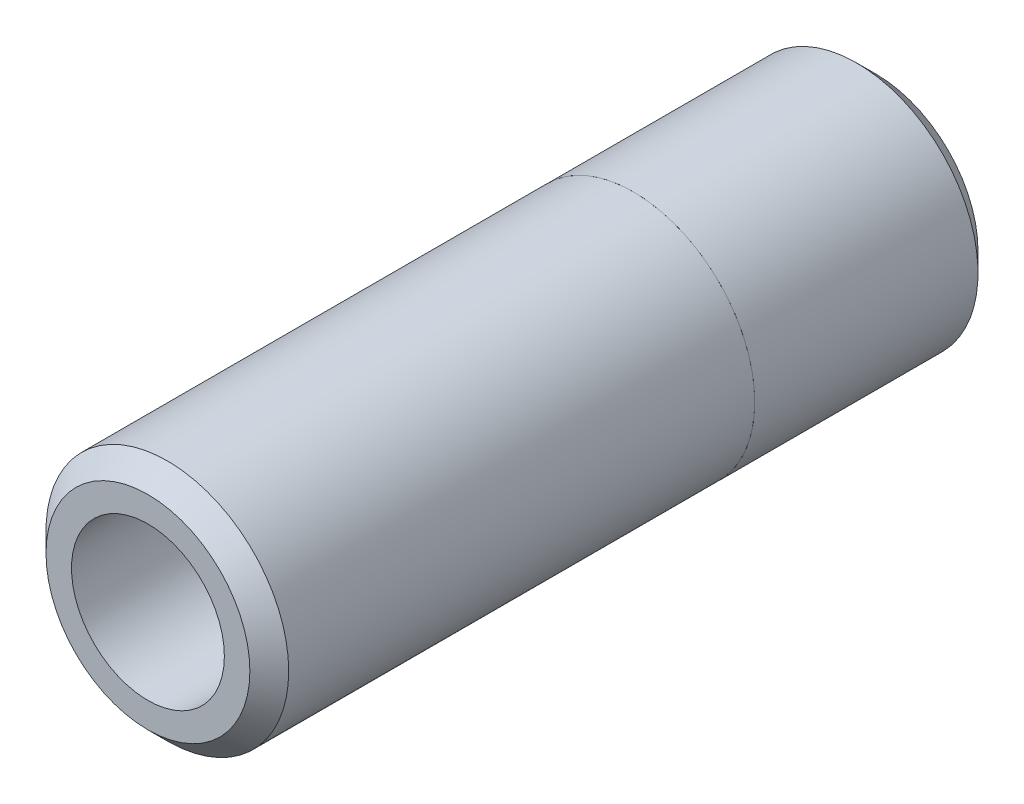
SolidWorks part; units mm, degrees
material "Delrin 2700 NC010, Low Viscosity Acetal Copolymer (SS)"
ref_plane "Front Plane" through (0, 0, 0) normal (0, 0, 1) x (1, 0, 0)
ref_plane "Top Plane" through (0, 0, 0) normal (0, 1, 0) x (1, 0, 0)
ref_plane "Right Plane" through (0, 0, 0) normal (1, 0, 0) x (0, 0, -1)
sketch "Sketch1" plane through (0, 0, 0) normal (0, 0, 1) x (1, 0, 0)
  circle A0 centre (0, 0) radius 4.7625
  dimension "D1" = 9.525
extrude "Side With Hole" add sketch "Sketch1" along normal blind 19.05
sketch "Sketch2" plane through (0, 0, 0) normal (0, 0, -1) x (-1, 0, 0)
  circle A1 centre (0, 0) radius 4.7625
  circle A2 centre (0, 0) radius 4.7625
  dimension "D1" = 0
extrude "Side Without Hole" add sketch "Sketch2" along normal blind 9.525 separate body
hole_wizard "Ø6.0 (6) Diameter Hole1" positions "Sketch3" profile "Sketch4" hole size "Ø6.0" standard "ANSI Metric"
sketch "Sketch3" plane through (0, 0, 19.05) normal (0, 0, 1) x (1, 0, 0)
  point P0 (0, 0)
sketch "Sketch4" plane through (0, 0, 19.05) normal (1, 0, 0) x (0, -1, 0)
  line L0 (0, 0) -> (0, 22.7576)
  line L1 (0, 22.7576) -> (3, 20.955)
  line L2 (3, 20.955) -> (3, 0)
  line L5 (3, 0) -> (0, 0)
  line L10 (0, 22.7576) -> (-3, 20.955) construction
  line L11 (0, -6.35) -> (0, 107.95) construction
  dimension "Hole Dia." = 6
  dimension "Hole Depth" = 20.955
  dimension "Drill Angle" = 118
chamfer "Chamfer1" distance 0.762 angle 45 1 edges at (-4.7625, 0, -9.525)
chamfer "Chamfer2" distance 0.762 angle 45 1 edges at (4.7625, 0, 19.05)
